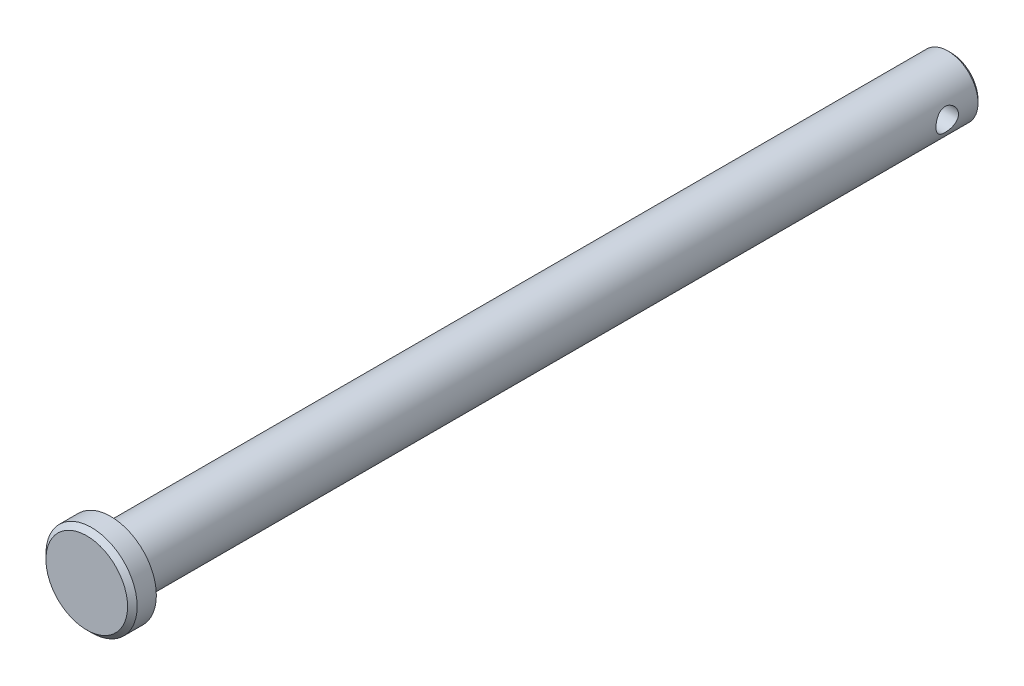
SolidWorks part; units mm, degrees
material "6061 Alloy"
ref_plane "Front" through (0, 0, 0) normal (0, 0, 1) x (1, 0, 0)
ref_plane "Top" through (0, 0, 0) normal (0, 1, 0) x (1, 0, 0)
ref_plane "Right" through (0, 0, 0) normal (1, 0, 0) x (0, 0, -1)
sketch "Sketch1" plane through (0, 0, 0) normal (0, 0, 1) x (1, 0, 0)
  circle A0 centre (0, 0) radius 3.175
  point P3 (0, 3.175)
  point P4 (0, -3.175)
  dimension "dia" = 6.35
extrude "Extrude1" add sketch "Sketch1" along normal mid plane 88.9
sketch "Sketch2" plane through (0, 0, 44.45) normal (0, 0, 1) x (1, 0, 0)
  circle A0 centre (0, 0) radius 4.826
  dimension "head dia" = 9.652
extrude "Extrude2" add sketch "Sketch2" along normal blind 2.54
chamfer "Chamfer1" distance 0.508 angle 45 1 edges at (4.826, 0, 46.99)
sketch "Sketch3" plane through (0, 0, 0) normal (1, 0, 0) x (0, 0, -1)
  line L0 (-44.45, -3.175) -> (-44.45, 3.175) construction
  circle A0 centre (40.8781, 0) radius 1.1906
  point P2 (39.6875, 0)
  dimension "hole dia" = 2.3813
  dimension "useable Lg" = 84.1375
extrude "Extrude3" cut sketch "Sketch3" against normal through all and the other way through all
chamfer "Chamfer2" distance 0.3175 angle 45 1 edges at (3.175, 0, -44.45)
ref_plane "Plane1" through (0, 0, -40.8781) normal (0, 0, 1) x (1, 0, 0)
sketch "Sketch8" plane through (0, 0, 0) normal (1, 0, 0) x (0, 0, -1)
  line L0 (-46.99, 4.318) -> (-46.99, -4.318) construction
  line L1 (-46.482, -4.826) -> (-44.45, -4.826) construction
  line L2 (44.45, -2.8575) -> (44.45, 2.8575) construction
  point P0 (-46.99, 4.826)
  point P1 (-44.45, 4.826)
  point P5 (44.45, 3.175)
  point P8 (-46.99, -4.826)
  point P9 (44.45, -3.175)
equation "\"D1@Chamfer1\" = \"head ht@Extrude2\" * .2"
equation "\"D1@Chamfer2\" = \"dia@Sketch1\" * .05"
